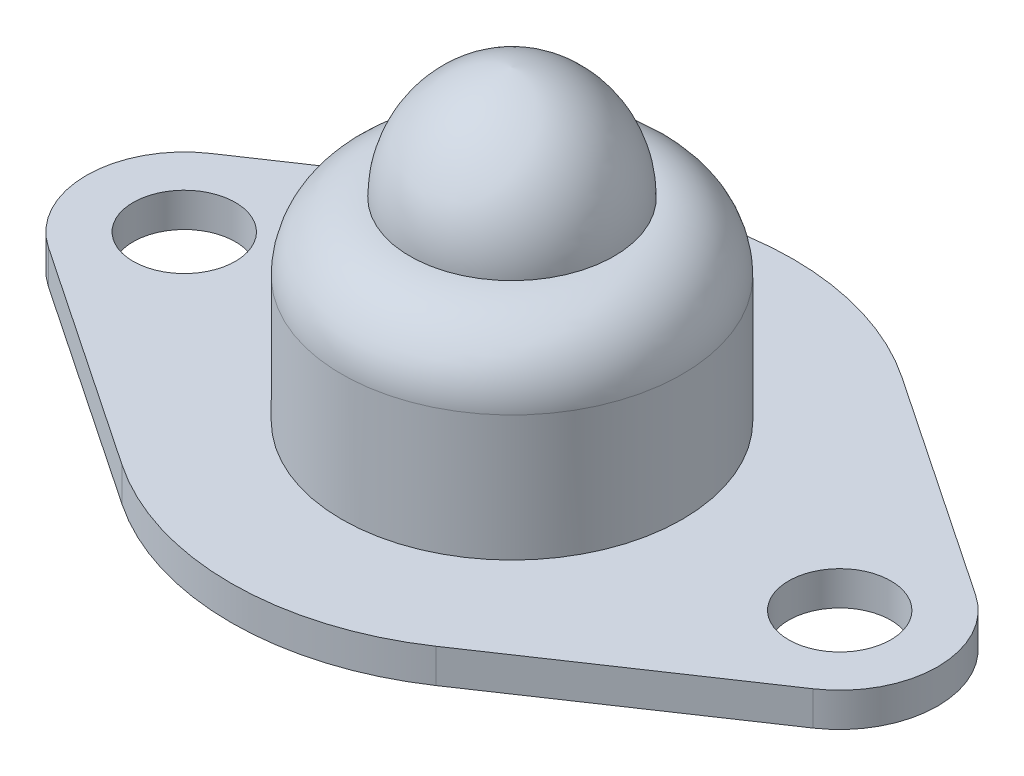
SolidWorks part; units mm, degrees
material "PET"
ref_plane "Front" through (0, 0, 0) normal (0, 0, 1) x (1, 0, 0)
ref_plane "Top" through (0, 0, 0) normal (0, 1, 0) x (1, 0, 0)
ref_plane "Right" through (0, 0, 0) normal (1, 0, 0) x (0, 0, -1)
sketch "Sketch2" plane through (0, 0, 0) normal (0, 1, 0) x (1, 0, 0)
  line L0 (-9.625, 0) -> (9.625, 0) construction
  line L1 (-4.6071, 6.8437) -> (-11.2305, 2.3849)
  line L2 (-9.625, 0) -> (-12.5, 0) construction
  line L3 (-11.2305, -2.3849) -> (-4.6071, -6.8437)
  line L5 (4.6071, -6.8437) -> (11.2305, -2.3849)
  line L7 (11.2305, 2.3849) -> (4.6071, 6.8437)
  circle A0 centre (-9.625, 0) radius 1.5
  circle A1 centre (9.625, 0) radius 1.5
  arc A2 (-4.6071, -6.8437) -> (4.6071, -6.8437) centre (0, 0) ccw
  arc A3 (4.6071, 6.8437) -> (-4.6071, 6.8437) centre (0, 0) ccw
  arc A4 (11.2305, 2.3849) -> (11.2305, -2.3849) centre (9.625, 0) cw
  arc A5 (-11.2305, 2.3849) -> (-11.2305, -2.3849) centre (-9.625, 0) ccw
  dimension "D1" = 19.25
  dimension "Flange Wd" = 16.5
  dimension "Bolt Hole Dia" = 3
  dimension "Flange Lg" = 25
extrude "Boss.-Extru.1" add sketch "Sketch2" along normal blind 1
sketch "Esquisse1" plane through (0, 0, 0) normal (0, 0, 1) x (1, 0, 0)
  line L0 (-5, 1) -> (-5, 4.6902)
  line L1 (0, -1.1482) -> (0, 15.9741) construction
  line L2 (-5, 4.6902) -> (0, 4.6902)
  line L3 (-5, 1) -> (0, 1)
  line L4 (4.6071, 1) -> (-4.6071, 1) construction
  line L6 (0, 6.6902) -> (-2.9967, 6.6902)
  arc A0 (-5, 4.6902) -> (-2.9967, 6.6902) centre (-3, 4.6902) cw
  arc A1 (-2.9967, 6.6902) -> (0, 10) centre (0.3294, 6.6902) cw
  dimension "D1" = 9
  dimension "D2" = 2
  dimension "D3" = 5
revolve "Révolution1" add sketch "Esquisse1" angle 360 about L1
